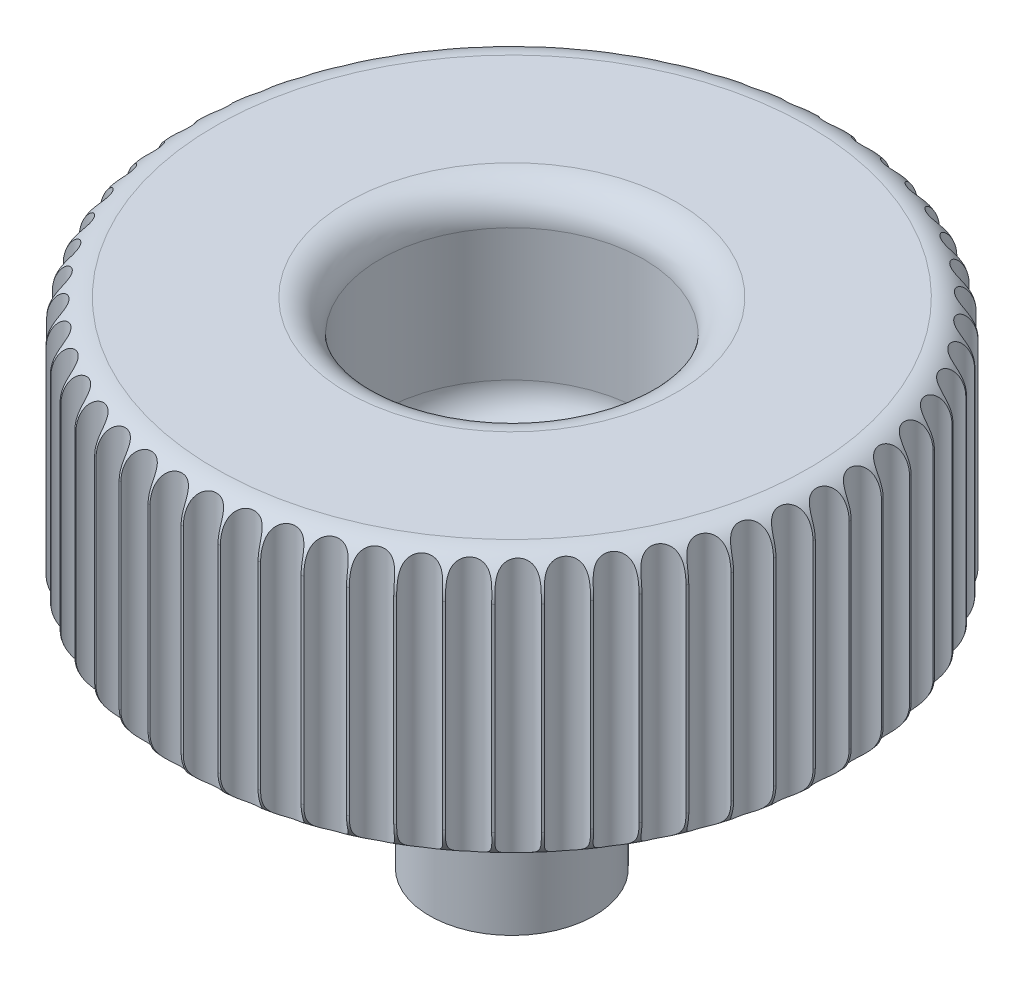
SolidWorks part; units mm, degrees
ref_plane "Front Plane" through (0, 0, 0) normal (0, 0, 1) x (1, 0, 0)
ref_plane "Top Plane" through (0, 0, 0) normal (0, 1, 0) x (1, 0, 0)
ref_plane "Right Plane" through (0, 0, 0) normal (1, 0, 0) x (0, 0, -1)
sketch "Sketch1" plane through (0, 0, 0) normal (1, 0, 0) x (0, 0, -1)
  line L0 (0, 0) -> (0, 2)
  line L1 (0, 2) -> (3, 2)
  line L2 (4, 3) -> (4, 7)
  line L3 (5, 8) -> (9, 8)
  line L4 (10, 7) -> (10, 1)
  line L5 (9, 0) -> (8, 0)
  line L6 (8, 0) -> (8, 5.2941)
  line L7 (7, 6.2941) -> (6, 6.2941)
  line L8 (5, 5.2941) -> (5, 1)
  line L9 (4, 0) -> (0, 0)
  arc A0 (10, 1) -> (9, 0) centre (9, 1) cw
  arc A1 (5, 1) -> (4, 0) centre (4, 1) cw
  arc A2 (3, 2) -> (4, 3) centre (3, 3) ccw
  arc A3 (8, 5.2941) -> (7, 6.2941) centre (7, 5.2941) ccw
  arc A4 (6, 6.2941) -> (5, 5.2941) centre (6, 5.2941) ccw
  arc A5 (4, 7) -> (5, 8) centre (5, 7) cw
  arc A6 (9, 8) -> (10, 7) centre (9, 7) cw
  point P13 (10, 0)
  point P20 (8, 6.2941)
  point P23 (5, 6.2941)
  point P26 (4, 8)
  point P29 (10, 8)
  dimension "D8" = 1
  dimension "D1" = 2
  dimension "D2" = 8
  dimension "D3" = 3
  dimension "D4" = 1
  dimension "D5" = 6
  dimension "D6" = 10
  dimension "D7" = 2
revolve "Revolve1" add sketch "Sketch1" angle 360 about L0
sketch "Sketch2" plane through (0, 0, 0) normal (0, -1, 0) x (1, 0, 0)
  circle A0 centre (0, 0) radius 2.5
  dimension "D1" = 5
extrude "Boss-Extrude1" add sketch "Sketch2" along normal blind 7
sketch "Sketch3" plane through (0, 0, 0) normal (0, 1, 0) x (1, 0, 0)
  line L0 (0, 0) -> (0, 10) construction
  circle A1 centre (0, 10) radius 0.5
  circle A2 centre (1.0629, 9.9433) radius 0.5
  circle A3 centre (2.1138, 9.774) radius 0.5
  circle A4 centre (3.1408, 9.494) radius 0.5
  circle A5 centre (4.1321, 9.1063) radius 0.5
  circle A6 centre (5.0767, 8.6155) radius 0.5
  circle A7 centre (5.9637, 8.0271) radius 0.5
  circle A8 centre (6.7831, 7.3477) radius 0.5
  circle A9 centre (7.5257, 6.5851) radius 0.5
  circle A10 centre (8.183, 5.7479) radius 0.5
  circle A11 centre (8.7476, 4.8455) radius 0.5
  circle A12 centre (9.2131, 3.8882) radius 0.5
  circle A13 centre (9.5742, 2.8869) radius 0.5
  circle A14 centre (9.8268, 1.8529) radius 0.5
  circle A15 centre (9.9681, 0.7979) radius 0.5
  circle A16 centre (9.9965, -0.2662) radius 0.5
  circle A17 centre (9.9115, -1.3273) radius 0.5
  circle A18 centre (9.7143, -2.3733) radius 0.5
  circle A19 centre (9.407, -3.3924) radius 0.5
  circle A20 centre (8.9931, -4.3731) radius 0.5
  circle A21 centre (8.4773, -5.3042) radius 0.5
  circle A22 centre (7.8655, -6.1752) radius 0.5
  circle A23 centre (7.1646, -6.9763) radius 0.5
  circle A24 centre (6.3824, -7.6983) radius 0.5
  circle A25 centre (5.528, -8.3331) radius 0.5
  circle A26 centre (4.6109, -8.8735) radius 0.5
  circle A27 centre (3.6416, -9.3134) radius 0.5
  circle A28 centre (2.631, -9.6477) radius 0.5
  circle A29 centre (1.5906, -9.8727) radius 0.5
  circle A30 centre (0.5322, -9.9858) radius 0.5
  circle A31 centre (-0.5322, -9.9858) radius 0.5
  circle A32 centre (-1.5906, -9.8727) radius 0.5
  circle A33 centre (-2.631, -9.6477) radius 0.5
  circle A34 centre (-3.6416, -9.3134) radius 0.5
  circle A35 centre (-4.6109, -8.8735) radius 0.5
  circle A36 centre (-5.528, -8.3331) radius 0.5
  circle A37 centre (-6.3824, -7.6983) radius 0.5
  circle A38 centre (-7.1646, -6.9763) radius 0.5
  circle A39 centre (-7.8655, -6.1752) radius 0.5
  circle A40 centre (-8.4773, -5.3042) radius 0.5
  circle A41 centre (-8.9931, -4.3731) radius 0.5
  circle A42 centre (-9.407, -3.3924) radius 0.5
  circle A43 centre (-9.7143, -2.3733) radius 0.5
  circle A44 centre (-9.9115, -1.3273) radius 0.5
  circle A45 centre (-9.9965, -0.2662) radius 0.5
  circle A46 centre (-9.9681, 0.7979) radius 0.5
  circle A47 centre (-9.8268, 1.8529) radius 0.5
  circle A48 centre (-9.5742, 2.8869) radius 0.5
  circle A49 centre (-9.2131, 3.8882) radius 0.5
  circle A50 centre (-8.7476, 4.8455) radius 0.5
  circle A51 centre (-8.183, 5.7479) radius 0.5
  circle A52 centre (-7.5257, 6.5851) radius 0.5
  circle A53 centre (-6.7831, 7.3477) radius 0.5
  circle A54 centre (-5.9637, 8.0271) radius 0.5
  circle A55 centre (-5.0767, 8.6155) radius 0.5
  circle A56 centre (-4.1321, 9.1063) radius 0.5
  circle A57 centre (-3.1408, 9.494) radius 0.5
  circle A58 centre (-2.1138, 9.774) radius 0.5
  circle A59 centre (-1.0629, 9.9433) radius 0.5
  circle A60 centre (0, 0) radius 10 construction
  point P123 (0, 0)
  dimension "D1" = 1
  dimension "D2" = 59
extrude "Cut-Extrude1" cut sketch "Sketch3" along normal blind 12
ref_plane "Plane1" through (0, 1, 0) normal (0, 1, 0) x (1, 0, 0)
